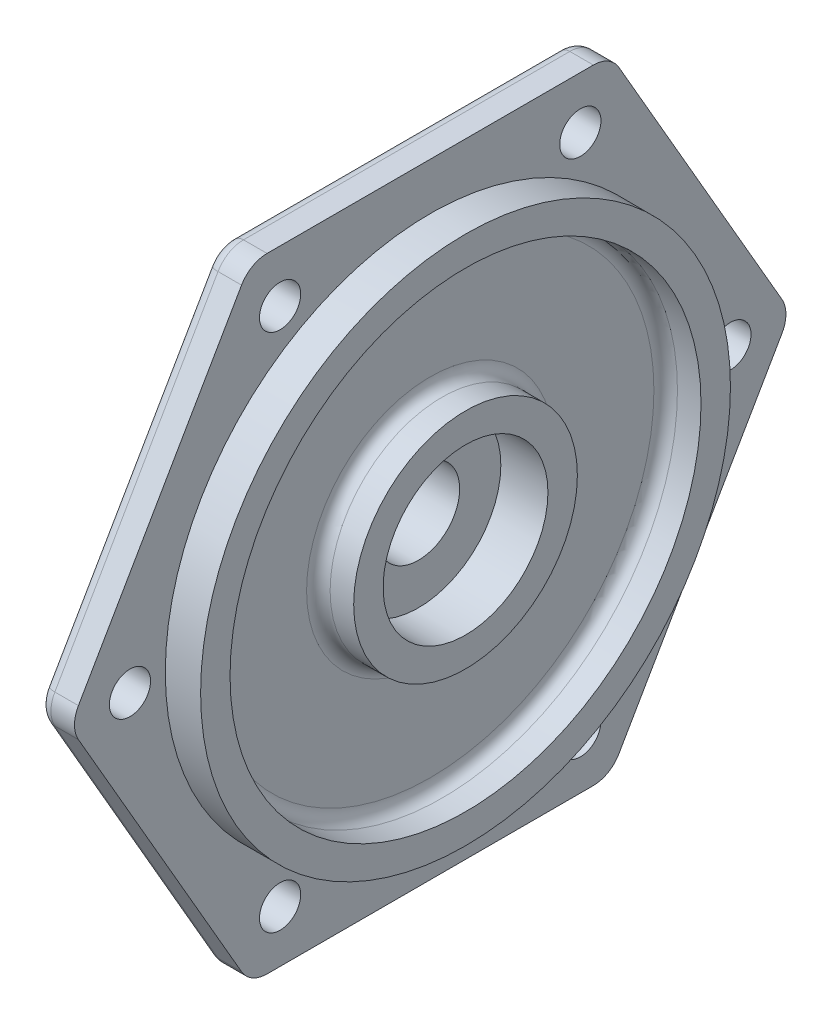
SolidWorks part; units mm, degrees
material "6061 Alloy"
ref_plane "Front Plane" through (0, 0, 0) normal (0, 0, 1) x (1, 0, 0)
ref_plane "Top Plane" through (0, 0, 0) normal (0, 1, 0) x (1, 0, 0)
ref_plane "Right Plane" through (0, 0, 0) normal (1, 0, 0) x (0, 0, -1)
sketch "Sketch1" plane through (0, 0, 0) normal (1, 0, 0) x (0, 0, -1)
  line L0 (-124.0088, 0) -> (109.6932, 0) construction
  line L1 (59.7558, 2.5) -> (32.0429, 50.5)
  line L2 (27.7128, 53) -> (-27.7128, 53)
  line L3 (-32.0429, 50.5) -> (-59.7558, 2.5)
  line L4 (-59.7558, -2.5) -> (-32.0429, -50.5)
  line L5 (-27.7128, -53) -> (27.7128, -53)
  line L6 (32.0429, -50.5) -> (59.7558, -2.5)
  line L7 (0, 0) -> (-51, 0) construction
  circle A0 centre (0, 0) radius 53 construction
  arc A1 (27.7128, 53) -> (32.0429, 50.5) centre (27.7128, 48) cw
  arc A2 (59.7558, 2.5) -> (59.7558, -2.5) centre (55.4256, 0) cw
  arc A3 (32.0429, -50.5) -> (27.7128, -53) centre (27.7128, -48) cw
  arc A4 (-27.7128, -53) -> (-32.0429, -50.5) centre (-27.7128, -48) cw
  arc A5 (-59.7558, -2.5) -> (-59.7558, 2.5) centre (-55.4256, 0) cw
  arc A6 (-32.0429, 50.5) -> (-27.7128, 53) centre (-27.7128, 48) cw
  circle A7 centre (0, 0) radius 51 construction
  circle A8 centre (-51, 0) radius 3.5
  circle A9 centre (-25.5, 44.1673) radius 3.5
  circle A10 centre (25.5, 44.1673) radius 3.5
  circle A11 centre (51, 0) radius 3.5
  circle A12 centre (25.5, -44.1673) radius 3.5
  circle A13 centre (-25.5, -44.1673) radius 3.5
  point P15 (61.1991, 0)
  dimension "D2" = 5
  dimension "D1" = 106
  dimension "D3" = 102
  dimension "D4" = 7
  dimension "D6" = 51
  dimension "D7" = 51
  dimension "D5" = 6
extrude "Boss-Extrude1" add sketch "Sketch1" along normal blind 6
fillet "Fillet1" radius 2 12 edges at (0, 52.3301, -30.2128) (0, 26.5, -45.8993) (0, 0, -60.4256) (0, -26.5, -45.8993) (0, -52.3301, -30.2128) (0, -53, 0) (0, -52.3301, 30.2128) (0, -26.5, 45.8993) (0, 0, 60.4256) (0, 26.5, 45.8993) (0, 52.3301, 30.2128) (0, 53, 0)
sketch "Sketch2" plane through (6, 0, 0) normal (1, 0, 0) x (0, 0, -1)
  circle A0 centre (0, 0) radius 45
  circle A1 centre (0, 0) radius 40
  dimension "D1" = 90
  dimension "D2" = 80
extrude "Boss-Extrude2" add sketch "Sketch2" along normal blind 6
fillet "Fillet2" radius 2 1 edges at (6, 0, -40)
sketch "Sketch3" plane through (6, 0, 0) normal (1, 0, 0) x (0, 0, -1)
  circle A0 centre (0, 0) radius 19
  circle A1 centre (0, 0) radius 14
  dimension "D1" = 38
  dimension "D2" = 28
extrude "Boss-Extrude3" add sketch "Sketch3" along normal blind 6
fillet "Fillet3" radius 2 1 edges at (6, 0, 19)
sketch "Sketch4" plane through (6, 0, 0) normal (1, 0, 0) x (0, 0, -1)
  circle A0 centre (0, 0) radius 14
  dimension "D1" = 28
extrude "Cut-Extrude1" cut sketch "Sketch4" against normal blind 2
sketch "Sketch6" plane through (0, 0, 0) normal (-1, 0, 0) x (0, 0, 1)
  circle A0 centre (0, 0) radius 23
  dimension "D1" = 46
extrude "Boss-Extrude4" add sketch "Sketch6" along normal blind 4
sketch "Sketch7" plane through (4, 0, 0) normal (1, 0, 0) x (0, 0, -1)
  circle A0 centre (0, 0) radius 7
  dimension "D1" = 14
extrude "Cut-Extrude2" cut sketch "Sketch7" against normal through all and the other way through all
